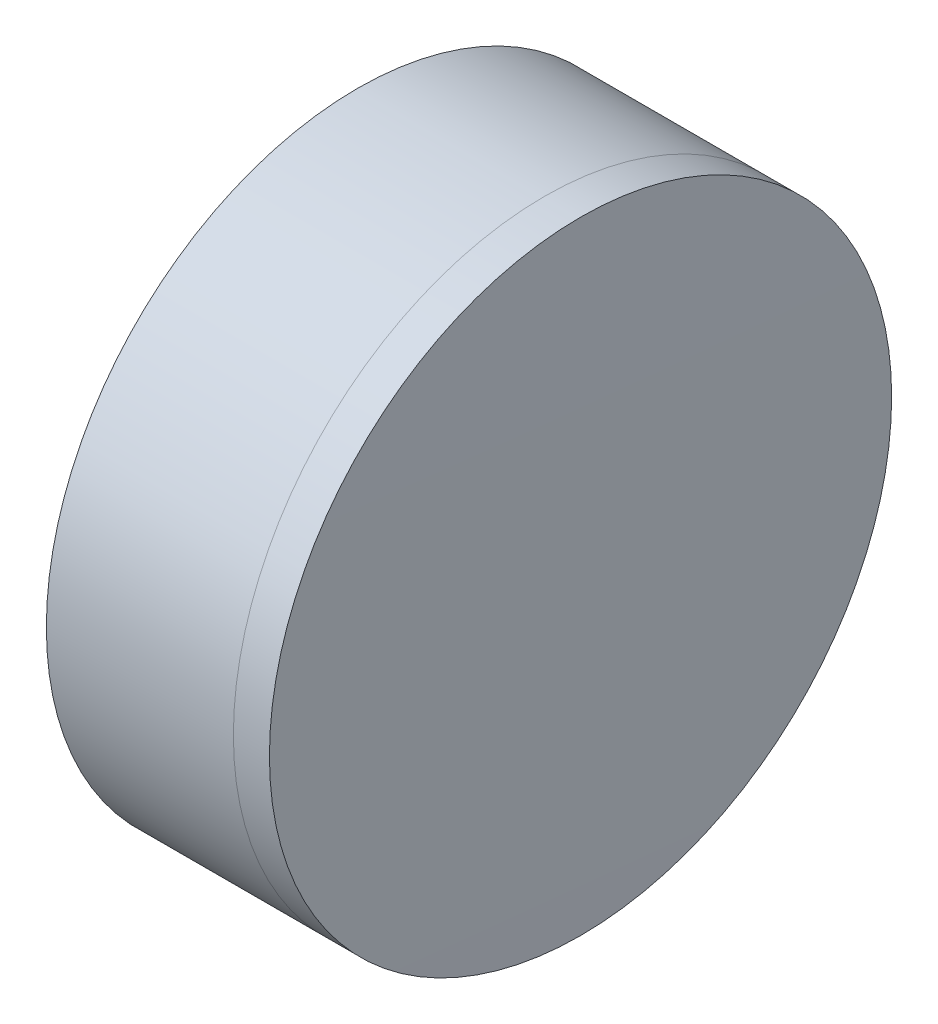
SolidWorks part; units mm, degrees
ref_plane "前视基准面" through (0, 0, 0) normal (0, 0, 1) x (1, 0, 0)
ref_plane "上视基准面" through (0, 0, 0) normal (0, 1, 0) x (1, 0, 0)
ref_plane "右视基准面" through (0, 0, 0) normal (1, 0, 0) x (0, 0, -1)
sketch "草图1" plane through (0, 0, 0) normal (0, 1, 0) x (1, 0, 0)
  line L0 (-185.2745, 0) -> (432.0321, 0) construction
  line L1 (147.2621, 12.7) -> (154.8968, 12.7)
  line L4 (147.2621, -12.7) -> (154.8968, -12.7)
  arc A0 (147.2621, -12.7) -> (147.2621, 12.7) centre (123.3788, 0) ccw
  arc A1 (154.8968, 12.7) -> (154.8968, -12.7) centre (186.3388, 0) ccw
  point P6 (150.4288, 0)
  point P8 (152.4288, 0)
  dimension "D3" = 12.7
  dimension "D4" = 2
  dimension "D1" = 27.05
  dimension "D5" = 33.91
  dimension "D2" = 12.7
revolve "旋转1" add sketch "草图1" angle 360 about L0
sketch "草图2" plane through (0, 0, 0) normal (0, 1, 0) x (1, 0, 0)
  line L2 (147.2621, 0) -> (272.9951, 0) construction
  line L3 (147.2621, -12.7) -> (147.2621, 12.7) construction
  line L6 (154.8968, 12.7) -> (156.3682, 12.7)
  line L7 (154.8968, -12.7) -> (156.3682, -12.7)
  arc A0 (156.3682, -12.7) -> (156.3682, 12.7) centre (-1174.0712, 0) ccw
  arc A2 (154.8968, 12.7) -> (154.8968, -12.7) centre (186.3388, 0) ccw construction
  arc A3 (154.8968, 12.7) -> (154.8968, -12.7) centre (186.3388, 0) ccw
  point P2 (108.741, 0)
  point P8 (152.4288, 0)
  point P9 (-68.6416, 0)
  point P13 (-1125.7008, 0)
  point P15 (156.4288, 0)
  dimension "D1" = 1330.5
  dimension "D2" = 4
revolve "旋转3" add sketch "草图2" angle 360 about L2
